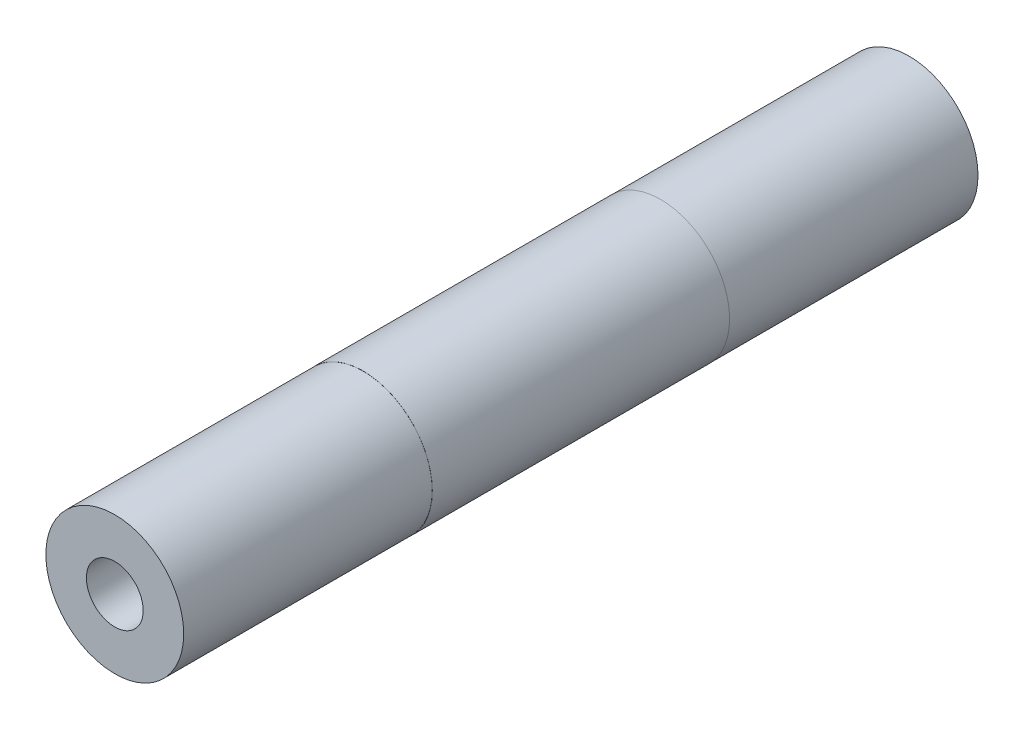
SolidWorks part; units mm, degrees
material "SS 304 (Default)"
ref_plane "Front Plane" through (0, 0, 0) normal (0, 0, 1) x (1, 0, 0)
ref_plane "Top Plane" through (0, 0, 0) normal (0, 1, 0) x (1, 0, 0)
ref_plane "Right Plane" through (0, 0, 0) normal (1, 0, 0) x (0, 0, -1)
sketch "Sketch1" plane through (0, 0, 0) normal (0, 0, 1) x (1, 0, 0)
  circle A0 centre (0, 0) radius 7.9375
  dimension "Diameter" = 15.875
extrude "Extrude1" add sketch "Sketch1" along normal mid plane 91.3384
hole_wizard "5/16-18 Tapped Hole1" positions "Sketch2" profile "Sketch3" tap size "5/16-18" standard "ANSI Inch"
sketch "Sketch2" plane through (0, 0, 45.6692) normal (0, 0, 1) x (1, 0, 0)
  point P0 (0, 0)
sketch "Sketch3" plane through (0, 0, 45.6692) normal (1, 0, 0) x (0, -1, 0)
  line L0 (0, 0) -> (0, 22.0271)
  line L1 (0, 22.0271) -> (3.2639, 20.066)
  line L2 (3.2639, 20.066) -> (3.2639, 0)
  line L5 (3.2639, 0) -> (0, 0)
  line L10 (0, 22.0271) -> (-3.2639, 20.066) construction
  line L11 (0, -6.35) -> (0, 107.95) construction
  dimension "Tap Drill Dia." = 6.5278
  dimension "Tap Drill Depth" = 20.066
  dimension "Drill Angle" = 118
cosmetic thread "Hole Thread1" parameters "D1"=16.002, "D2"=7.9375
hole_wizard "5/16-18 Tapped Hole2" positions "Sketch4" profile "Sketch5" tap size "5/16-18" standard "ANSI Inch"
sketch "Sketch4" plane through (0, 0, -45.6692) normal (0, 0, -1) x (-1, 0, 0)
  point P0 (0, 0)
sketch "Sketch5" plane through (0, 0, -45.6692) normal (1, 0, 0) x (0, 1, 0)
  line L0 (0, 0) -> (0, 22.0271)
  line L1 (0, 22.0271) -> (3.2639, 20.066)
  line L2 (3.2639, 20.066) -> (3.2639, 0)
  line L5 (3.2639, 0) -> (0, 0)
  line L10 (0, 22.0271) -> (-3.2639, 20.066) construction
  line L11 (0, -6.35) -> (0, 107.95) construction
  dimension "Tap Drill Dia." = 6.5278
  dimension "Tap Drill Depth" = 20.066
  dimension "Drill Angle" = 118
cosmetic thread "Hole Thread2" parameters "D1"=16.002, "D2"=7.9375
sketch "Sketch6" plane through (0, 0, 45.6692) normal (0, 0, 1) x (1, 0, 0)
  circle A0 centre (0, 0) radius 7.9248
  circle A1 centre (0, 0) radius 7.9375 construction
  circle A2 centre (0, 0) radius 7.9375
  dimension "D1" = 15.8496
extrude "Cut-Extrude1" cut sketch "Sketch6" against normal blind 28.575
mirror "Mirror1" about plane through (0, 0, 0) normal (0, 0, 1) of "Cut-Extrude1"
